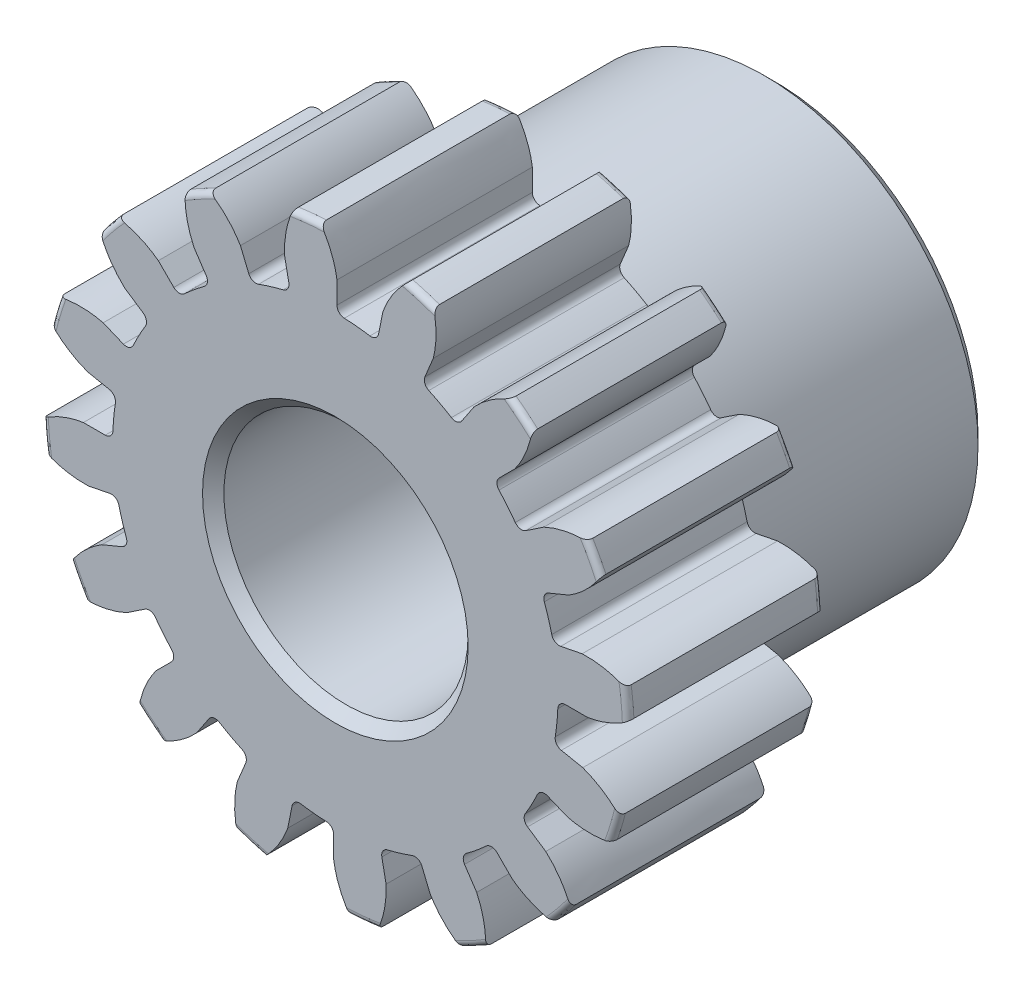
SolidWorks part; units mm, degrees
ref_plane "Front" through (0, 0, 0) normal (0, 0, 1) x (1, 0, 0)
ref_plane "Top" through (0, 0, 0) normal (0, 1, 0) x (1, 0, 0)
ref_plane "Right" through (0, 0, 0) normal (1, 0, 0) x (0, 0, -1)
sketch "Sketch1" plane through (0, 0, 0) normal (0, 0, 1) x (1, 0, 0)
  line L0 (-203.2, 0) -> (203.2, 0) construction
  circle A0 centre (0, 0) radius 9.525
  circle A1 centre (0, 0) radius 8.4582 construction
  circle A3 centre (0, 0) radius 7.2349 construction
  dimension "D1" = 1.2233
  dimension "OD" = 19.05
  dimension "Ptich Dia" = 16.9164
  dimension "D2" = 2.2901
  dimension "Root Dia" = 14.4699
  dimension "D3" = 1.0668
  dimension "Number of Teeth" = 406.4
extrude "Boss-Extrude1" add sketch "Sketch1" against normal blind 6.35
sketch "Sketch2" plane through (0, 0, 0) normal (1, 0, 0) x (0, 0, -1)
  line L0 (6.35, 0) -> (14.2875, 0)
  line L1 (6.35, 0) -> (6.35, 6.9453)
  line L2 (6.35, 6.9453) -> (14.2875, 6.9453)
  line L3 (14.2875, 6.9453) -> (14.2875, 0)
  point P5 (14.2875, -6.9453)
  dimension "Face Wd" = 6.35
  dimension "B Hub Dia" = 13.8906
  dimension "D O'all Lg." = 14.2875
revolve "Revolve1" add sketch "Sketch2" angle 360 about L0
fillet "Fillet2" radius 0.1905 3 edges at (9.525, 0, -6.35) (9.525, 0, 0) (6.9453, 0, -6.35)
sketch "Sketch3" plane through (0, 0, 0) normal (0, 0, 1) x (1, 0, 0)
  line L0 (0, 0) -> (0, 9.525) construction
  line L1 (-2.0503, 7.928) -> (0, 8.4582)
  line L2 (-9.5921, 8.4582) -> (9.5921, 8.4582) construction
  line L3 (-9.2865, 6.0565) -> (9.2865, 10.8599) construction
  line L4 (-2.0503, 7.928) -> (0, 0) construction
  line L5 (-5.0649, 6.4345) -> (0, 0) construction
  line L6 (-5.0649, 6.4345) -> (-0.7384, 9.8402) construction
  line L7 (-1.4297, 8.063) -> (0, 0) construction
  line L8 (-1.4297, 8.063) -> (0.03, 8.3218) construction
  arc A0 (-2.0503, 7.928) -> (-5.0649, 6.4345) centre (0, 0) ccw
  circle A1 centre (0, 0) radius 8.4582 construction
  circle A2 centre (0, 0) radius 8.1888 construction
  arc A3 (-2.0503, 7.928) -> (-1.4297, 8.063) centre (0, 0) cw
  circle A4 centre (0, 0) radius 9.525 construction
  point P6 (0, 8.4582)
  dimension "D1" = 2.1178
  dimension "Pressure Angle" = 14.5
  dimension "D2" = 3.3884
  dimension "D3" = 5.5062
  dimension "D4" = 0.6353
  dimension "D5" = 1.4824
sketch "Sketch4" plane through (0, 0, 0) normal (0, 0, 1) x (1, 0, 0)
  line L0 (0, 0) -> (0.8251, 8.3769) construction
  line L1 (0.0532, 8.1886) -> (0.0532, 7.2347)
  line L2 (0, 8.4582) -> (1.6501, 8.2957) construction
  line L3 (1.5453, 8.0417) -> (1.3592, 7.1061)
  line L4 (0.0532, 7.2347) -> (0, 0) construction
  line L5 (0, 0) -> (0, 9.525) construction
  arc A0 (1.3592, 7.1061) -> (0.0532, 7.2347) centre (0, 0) ccw
  arc A1 (0, 8.4582) -> (1.6501, 8.2957) centre (0, 0) cw construction
  circle A2 centre (0, 0) radius 8.4582 construction
  circle A3 centre (0, 0) radius 8.1888 construction
  circle A4 centre (0, 0) radius 7.2349 construction
  arc A5 (2.6439, 9.5071) -> (-0.7384, 9.8402) centre (0, 0) ccw
  spline S0 degree 2 poles (-0.7384, 9.8402) (-0.0855, 9.0997) (0.0532, 8.1886) knots 0 0 0 1 1 1
  spline S1 degree 2 poles (2.6439, 9.5071) (1.8592, 8.9082) (1.5453, 8.0417) knots 0 0 0 1 1 1
  dimension "D1" = 1.6608
extrude "Cut-Extrude1" cut sketch "Sketch4" against normal through all
fillet "Fillet1" radius 0.2491 2 edges at (1.3592, 7.1061, -3.175) (0.0532, 7.2347, -3.175)
pattern_circular "CirPattern1" count 16 over 360 about axis through (0, 0, -6.35) along (0, 0, 1) of "Cut-Extrude1", "Fillet1"
sketch "Sketch5" plane through (0, 0, 0) normal (0, 0, 1) x (1, 0, 0)
  circle A0 centre (0, 0) radius 3.9688
  circle A1 centre (0, 0) radius 3.9688 construction
  dimension "Bore Min" = 7.9375
  dimension "Bore Max" = 7.9375
extrude "Cut-Extrude2" cut sketch "Sketch5" against normal through all
chamfer "Chamfer1" distance 0.3473 angle 45 3 edges at (6.9453, 0, -14.2875) (3.9688, 0, 0) (3.9688, 0, -14.2875)
sketch "Pitch Dia" plane through (0, 0, 0) normal (0, 0, 1) x (1, 0, 0)
  circle A0 centre (0, 0) radius 8.4582 construction
  circle A1 centre (0, 0) radius 8.4582
equation "\"D1@Boss-Extrude1\" = \"Face Wd@Sketch2\""
equation "\"D2@Sketch3\" = \"D1@Sketch3\"*1.6"
equation "\"D3@Sketch3\" = \"D1@Sketch3\"+\"D2@Sketch3\""
equation "\"D4@Sketch3\" = \"D1@Sketch3\"*.3"
equation "\"D5@Sketch3\" = \"D1@Sketch3\"-\"D4@Sketch3\""
equation "\"D1@Sketch4\" = 1.5708/(\"Number of Teeth@Sketch1\"/\"Ptich Dia@Sketch1\")"
equation "\"D1@Chamfer1\" = \"B Hub Dia@Sketch2\"*.025"
equation "\"D1@CirPattern1\" = \"Number of Teeth@Sketch1\""
equation "\"D1@Fillet1\" = \"D1@Sketch4\"*.15"
equation "\"D1@Fillet2\" = \"OD@Sketch1\"*.01"
equation "\"D1@Sketch1\" = 1.157/(\"Number of Teeth@Sketch1\"/\"Ptich Dia@Sketch1\")"
